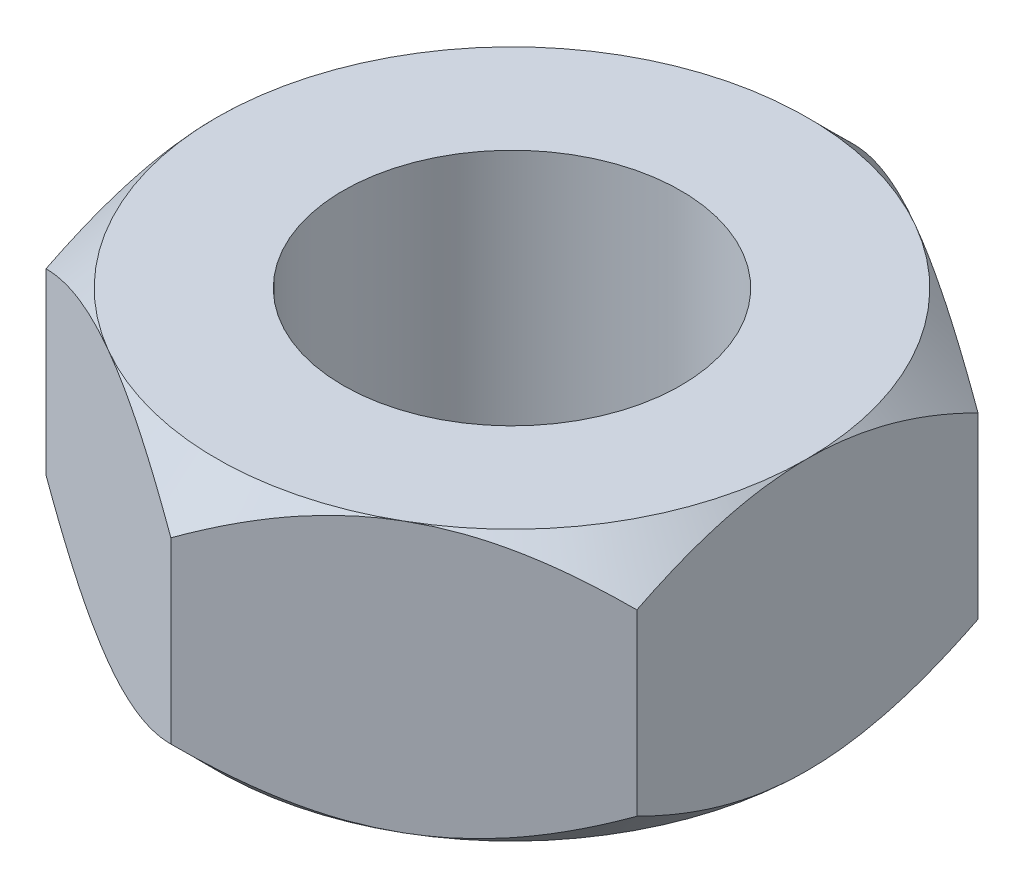
SolidWorks part; units mm, degrees
material "1023 Carbon Steel Sheet (SS)"
ref_plane "Front Plane" through (0, 0, 0) normal (0, 0, 1) x (1, 0, 0)
ref_plane "Top Plane" through (0, 0, 0) normal (0, 1, 0) x (1, 0, 0)
ref_plane "Right Plane" through (0, 0, 0) normal (1, 0, 0) x (0, 0, -1)
sketch "Sketch1" plane through (0, 0, 0) normal (0, 1, 0) x (1, 0, 0)
  line L1 (0, 4.0415) -> (-3.5, 2.0207)
  line L2 (-3.5, 2.0207) -> (-3.5, -2.0207)
  line L3 (-3.5, -2.0207) -> (0, -4.0415)
  line L4 (0, -4.0415) -> (3.5, -2.0207)
  line L5 (3.5, -2.0207) -> (3.5, 2.0207)
  line L6 (3.5, 2.0207) -> (0, 4.0415)
  circle A0 centre (0, 0) radius 3.5 construction
  circle A1 centre (0, 0) radius 2
  dimension "D2" = 4
  dimension "D1" = 7
extrude "Boss-Extrude1" add sketch "Sketch1" along normal blind 3.2
sketch "Sketch2" plane through (0, 3.2, 0) normal (0, 1, 0) x (1, 0, 0)
  circle A0 centre (0, 0) radius 3.5
  dimension "D1" = 7
extrude "Cut-Extrude1" cut sketch "Sketch2" against normal through all draft 45 flip side to cut
sketch "Sketch3" plane through (0, 0, 0) normal (0, -1, 0) x (1, 0, 0)
  circle A0 centre (0, 0) radius 3.5
  dimension "D1" = 7
extrude "Cut-Extrude2" cut sketch "Sketch3" against normal through all draft 45 flip side to cut
